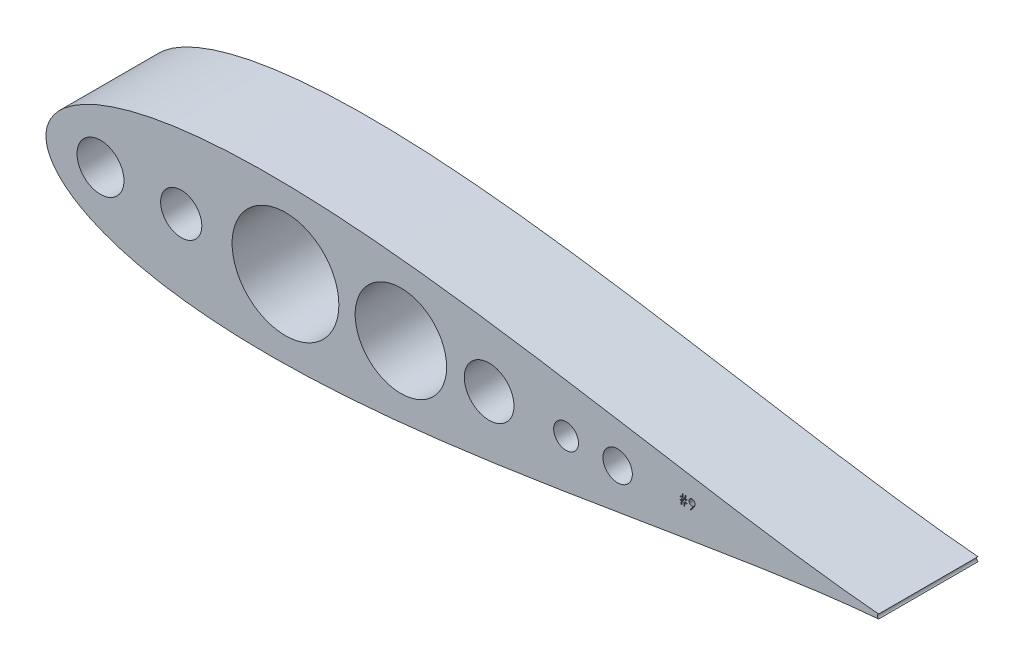
SolidWorks part; units mm, degrees
material "Polyurethane Foam Rigid"
ref_plane "Front Plane" through (0, 0, 0) normal (0, 0, 1) x (1, 0, 0)
ref_plane "Top Plane" through (0, 0, 0) normal (0, 1, 0) x (1, 0, 0)
ref_plane "Right Plane" through (0, 0, 0) normal (1, 0, 0) x (0, 0, -1)
sketch "Sketch2" plane through (0, 0, 0) normal (0, 0, 1) x (1, 0, 0)
  line L0 (258.6504, 1.1911) -> (258.6504, 0.8654)
  line L1 (258.6504, 0.8654) -> (257.6796, 0.8654)
  line L2 (257.6796, 0.8654) -> (257.416, -0.893)
  line L3 (257.416, -0.893) -> (257.0222, -0.893)
  line L4 (257.0222, -0.893) -> (257.2857, 0.8654)
  line L5 (257.2857, 0.8654) -> (256.2467, 0.8654)
  line L6 (256.2467, 0.8654) -> (255.9832, -0.893)
  line L7 (255.9832, -0.893) -> (255.5893, -0.893)
  line L8 (255.5893, -0.893) -> (255.8529, 0.8654)
  line L9 (255.8529, 0.8654) -> (255.0032, 0.8654)
  line L10 (255.0032, 0.8654) -> (255.0032, 1.1911)
  line L11 (255.0032, 1.1911) -> (255.9018, 1.1911)
  line L12 (255.9018, 1.1911) -> (256.0778, 2.3634)
  line L13 (256.0778, 2.3634) -> (255.1334, 2.3634)
  line L14 (255.1334, 2.3634) -> (255.1334, 2.689)
  line L15 (255.1334, 2.689) -> (256.1267, 2.689)
  line L16 (256.1267, 2.689) -> (256.3709, 4.3172)
  line L17 (256.3709, 4.3172) -> (256.7637, 4.3172)
  line L18 (256.7637, 4.3172) -> (256.5195, 2.689)
  line L19 (256.5195, 2.689) -> (257.5595, 2.689)
  line L20 (257.5595, 2.689) -> (257.8037, 4.3172)
  line L21 (257.8037, 4.3172) -> (258.1965, 4.3172)
  line L22 (258.1965, 4.3172) -> (257.9523, 2.689)
  line L23 (257.9523, 2.689) -> (258.7806, 2.689)
  line L24 (258.7806, 2.689) -> (258.7806, 2.3634)
  line L25 (258.7806, 2.3634) -> (257.9034, 2.3634)
  line L26 (257.9034, 2.3634) -> (257.7284, 1.1911)
  line L27 (257.7284, 1.1911) -> (258.6504, 1.1911)
  line L28 (257.5106, 2.3634) -> (256.4706, 2.3634)
  line L29 (256.4706, 2.3634) -> (256.2956, 1.1911)
  line L30 (256.2956, 1.1911) -> (257.3346, 1.1911)
  line L31 (257.3346, 1.1911) -> (257.5106, 2.3634)
  line L32 (260.7345, -1.0233) -> (260.3702, -0.7699)
  line L33 (260.3702, -0.7699) -> (261.7826, 1.2949)
  line L34 (261.7826, 1.2949) -> (261.5119, 1.2664)
  line L35 (261.5119, 1.2664) -> (261.2484, 1.2562)
  line L36 (261.2484, 1.2562) -> (261.0886, 1.2633)
  line L37 (261.0886, 1.2633) -> (260.936, 1.2837)
  line L38 (260.936, 1.2837) -> (260.7884, 1.3173)
  line L39 (260.7884, 1.3173) -> (260.648, 1.3651)
  line L40 (260.648, 1.3651) -> (260.5126, 1.4262)
  line L41 (260.5126, 1.4262) -> (260.3844, 1.5004)
  line L42 (260.3844, 1.5004) -> (260.2613, 1.589)
  line L43 (260.2613, 1.589) -> (260.1453, 1.6907)
  line L44 (260.1453, 1.6907) -> (260.0394, 1.8027)
  line L45 (260.0394, 1.8027) -> (259.9468, 1.9207)
  line L46 (259.9468, 1.9207) -> (259.8695, 2.0449)
  line L47 (259.8695, 2.0449) -> (259.8054, 2.1762)
  line L48 (259.8054, 2.1762) -> (259.7565, 2.3125)
  line L49 (259.7565, 2.3125) -> (259.7209, 2.456)
  line L50 (259.7209, 2.456) -> (259.6995, 2.6056)
  line L51 (259.6995, 2.6056) -> (259.6924, 2.7613)
  line L52 (259.6924, 2.7613) -> (259.7057, 2.974)
  line L53 (259.7057, 2.974) -> (259.7443, 3.1755)
  line L54 (259.7443, 3.1755) -> (259.8095, 3.3668)
  line L55 (259.8095, 3.3668) -> (259.9, 3.5469)
  line L56 (259.9, 3.5469) -> (260.015, 3.7138)
  line L57 (260.015, 3.7138) -> (260.1514, 3.8624)
  line L58 (260.1514, 3.8624) -> (260.3101, 3.9936)
  line L59 (260.3101, 3.9936) -> (260.4902, 4.1076)
  line L60 (260.4902, 4.1076) -> (260.6846, 4.1992)
  line L61 (260.6846, 4.1992) -> (260.8861, 4.2653)
  line L62 (260.8861, 4.2653) -> (261.0947, 4.304)
  line L63 (261.0947, 4.304) -> (261.3094, 4.3172)
  line L64 (261.3094, 4.3172) -> (261.5201, 4.304)
  line L65 (261.5201, 4.304) -> (261.7226, 4.2664)
  line L66 (261.7226, 4.2664) -> (261.917, 4.2022)
  line L67 (261.917, 4.2022) -> (262.1032, 4.1127)
  line L68 (262.1032, 4.1127) -> (262.2762, 3.9997)
  line L69 (262.2762, 3.9997) -> (262.4288, 3.8674)
  line L70 (262.4288, 3.8674) -> (262.5621, 3.7138)
  line L71 (262.5621, 3.7138) -> (262.6761, 3.5398)
  line L72 (262.6761, 3.5398) -> (262.7667, 3.3535)
  line L73 (262.7667, 3.3535) -> (262.8318, 3.1602)
  line L74 (262.8318, 3.1602) -> (262.8705, 2.9618)
  line L75 (262.8705, 2.9618) -> (262.8837, 2.7562)
  line L76 (262.8837, 2.7562) -> (262.8756, 2.5964)
  line L77 (262.8756, 2.5964) -> (262.8522, 2.4336)
  line L78 (262.8522, 2.4336) -> (262.8115, 2.2657)
  line L79 (262.8115, 2.2657) -> (262.7555, 2.0947)
  line L80 (262.7555, 2.0947) -> (262.7209, 2.0062)
  line L81 (262.7209, 2.0062) -> (262.6792, 1.9136)
  line L82 (262.6792, 1.9136) -> (262.6313, 1.8159)
  line L83 (262.6313, 1.8159) -> (262.5774, 1.7152)
  line L84 (262.5774, 1.7152) -> (262.5174, 1.6083)
  line L85 (262.5174, 1.6083) -> (262.4512, 1.4984)
  line L86 (262.4512, 1.4984) -> (262.3779, 1.3834)
  line L87 (262.3779, 1.3834) -> (262.2986, 1.2644)
  line L88 (262.2986, 1.2644) -> (260.7345, -1.0233)
  line L89 (261.3328, 1.7772) -> (261.4539, 1.7823)
  line L90 (261.4539, 1.7823) -> (261.5679, 1.7956)
  line L91 (261.5679, 1.7956) -> (261.6768, 1.819)
  line L92 (261.6768, 1.819) -> (261.7786, 1.8515)
  line L93 (261.7786, 1.8515) -> (261.8752, 1.8922)
  line L94 (261.8752, 1.8922) -> (261.9658, 1.9431)
  line L95 (261.9658, 1.9431) -> (262.0492, 2.0032)
  line L96 (262.0492, 2.0032) -> (262.1276, 2.0724)
  line L97 (262.1276, 2.0724) -> (262.1978, 2.1487)
  line L98 (262.1978, 2.1487) -> (262.2589, 2.228)
  line L99 (262.2589, 2.228) -> (262.3108, 2.3115)
  line L100 (262.3108, 2.3115) -> (262.3525, 2.399)
  line L101 (262.3525, 2.399) -> (262.3861, 2.4906)
  line L102 (262.3861, 2.4906) -> (262.4095, 2.5852)
  line L103 (262.4095, 2.5852) -> (262.4227, 2.6839)
  line L104 (262.4227, 2.6839) -> (262.4278, 2.7867)
  line L105 (262.4278, 2.7867) -> (262.4227, 2.8895)
  line L106 (262.4227, 2.8895) -> (262.4075, 2.9882)
  line L107 (262.4075, 2.9882) -> (262.381, 3.0829)
  line L108 (262.381, 3.0829) -> (262.3444, 3.1744)
  line L109 (262.3444, 3.1744) -> (262.2976, 3.2609)
  line L110 (262.2976, 3.2609) -> (262.2406, 3.3444)
  line L111 (262.2406, 3.3444) -> (262.1724, 3.4248)
  line L112 (262.1724, 3.4248) -> (262.094, 3.5001)
  line L113 (262.094, 3.5001) -> (262.0085, 3.5693)
  line L114 (262.0085, 3.5693) -> (261.919, 3.6293)
  line L115 (261.919, 3.6293) -> (261.8244, 3.6802)
  line L116 (261.8244, 3.6802) -> (261.7256, 3.7219)
  line L117 (261.7256, 3.7219) -> (261.6229, 3.7545)
  line L118 (261.6229, 3.7545) -> (261.515, 3.7779)
  line L119 (261.515, 3.7779) -> (261.4031, 3.7911)
  line L120 (261.4031, 3.7911) -> (261.286, 3.7962)
  line L121 (261.286, 3.7962) -> (261.17, 3.7911)
  line L122 (261.17, 3.7911) -> (261.0591, 3.7779)
  line L123 (261.0591, 3.7779) -> (260.9522, 3.7545)
  line L124 (260.9522, 3.7545) -> (260.8495, 3.7219)
  line L125 (260.8495, 3.7219) -> (260.7508, 3.6802)
  line L126 (260.7508, 3.6802) -> (260.6561, 3.6293)
  line L127 (260.6561, 3.6293) -> (260.5666, 3.5693)
  line L128 (260.5666, 3.5693) -> (260.4811, 3.5001)
  line L129 (260.4811, 3.5001) -> (260.4027, 3.4248)
  line L130 (260.4027, 3.4248) -> (260.3356, 3.3444)
  line L131 (260.3356, 3.3444) -> (260.2786, 3.2609)
  line L132 (260.2786, 3.2609) -> (260.2318, 3.1744)
  line L133 (260.2318, 3.1744) -> (260.1951, 3.0829)
  line L134 (260.1951, 3.0829) -> (260.1687, 2.9882)
  line L135 (260.1687, 2.9882) -> (260.1534, 2.8895)
  line L136 (260.1534, 2.8895) -> (260.1483, 2.7867)
  line L137 (260.1483, 2.7867) -> (260.1534, 2.6839)
  line L138 (260.1534, 2.6839) -> (260.1697, 2.5852)
  line L139 (260.1697, 2.5852) -> (260.1972, 2.4906)
  line L140 (260.1972, 2.4906) -> (260.2348, 2.399)
  line L141 (260.2348, 2.399) -> (260.2837, 2.3115)
  line L142 (260.2837, 2.3115) -> (260.3437, 2.228)
  line L143 (260.3437, 2.228) -> (260.4139, 2.1487)
  line L144 (260.4139, 2.1487) -> (260.4953, 2.0724)
  line L145 (260.4953, 2.0724) -> (260.5839, 2.0032)
  line L146 (260.5839, 2.0032) -> (260.6775, 1.9431)
  line L147 (260.6775, 1.9431) -> (260.7762, 1.8922)
  line L148 (260.7762, 1.8922) -> (260.878, 1.8515)
  line L149 (260.878, 1.8515) -> (260.9848, 1.819)
  line L150 (260.9848, 1.819) -> (261.0967, 1.7956)
  line L151 (261.0967, 1.7956) -> (261.2128, 1.7823)
  line L152 (261.2128, 1.7823) -> (261.3328, 1.7772)
  circle A0 centre (-41.275, 0) radius 12.0033
  circle A1 centre (0, 0) radius 10.541
  circle A2 centre (53.338, 0) radius 27.3042
  circle A3 centre (157.48, 0) radius 12.7
  circle A4 centre (223.2139, 0) radius 7.5268
  circle A5 centre (112.3573, 0) radius 23.3878
  arc A6 (356.7188, 1.1142) -> (356.7188, -1.1142) centre (357.2733, 0) ccw
  circle A7 centre (196.85, 0) radius 6.35
  spline S0 degree 3 poles (356.7188, 1.1142) (356.0338, 1.1732) (354.6472, 1.2925) (352.5436, 1.4844) (350.3911, 1.6885) (348.1899, 1.9056) (345.9398, 2.1355) (342.1802, 2.5322) (336.8158, 3.133) (329.9757, 3.9576) (323.0336, 4.8458) (313.8615, 6.0788) (302.3587, 7.7237) (288.6337, 9.805) (274.9221, 11.9724) (261.2201, 14.1999) (249.8068, 16.0865) (240.6774, 17.6031) (231.5482, 19.1212) (220.1361, 21.015) (206.4373, 23.2615) (192.7309, 25.462) (179.0142, 27.5966) (160.7077, 30.3278) (137.7851, 33.474) (110.2003, 36.6385) (87.0321, 38.5983) (68.5494, 39.6067) (54.5511, 40.05) (40.7774, 40.1228) (26.7493, 39.7655) (13.012, 38.9182) (-0.7973, 37.4621) (-12.0839, 35.6753) (-21.1417, 33.7674) (-27.9463, 32.0558) (-34.5959, 30.0529) (-41.1272, 27.6907) (-47.4261, 24.9354) (-53.538, 21.6252) (-58.3357, 18.2887) (-61.8002, 15.2095) (-64.1916, 12.6295) (-66.2213, 9.8466) (-67.8427, 6.7607) (-68.8989, 3.4741) (-69.2739, 0) (-68.8989, -3.4741) (-67.8427, -6.7606) (-66.2214, -9.8464) (-64.1918, -12.6293) (-61.8003, -15.2094) (-58.3359, -18.2886) (-53.538, -21.6252) (-47.4261, -24.9354) (-41.1274, -27.6906) (-34.5961, -30.0528) (-27.9465, -32.0558) (-21.1417, -33.7674) (-12.0839, -35.6753) (-0.7975, -37.4621) (13.0118, -38.9182) (26.749, -39.7655) (40.7772, -40.1228) (54.5508, -40.05) (68.5492, -39.6067) (87.0319, -38.5983) (110.2003, -36.6385) (137.7851, -33.474) (160.7077, -30.3278) (179.0142, -27.5966) (192.7309, -25.462) (206.4373, -23.2615) (220.1361, -21.015) (231.5482, -19.1212) (240.6774, -17.6031) (249.8068, -16.0865) (261.2201, -14.1999) (274.9221, -11.9724) (288.6337, -9.805) (302.3587, -7.7237) (313.8613, -6.0788) (323.0334, -4.8458) (329.9754, -3.9576) (336.8157, -3.1331) (342.9292, -2.4482) (348.1398, -1.9072) (352.4934, -1.4831) (355.3323, -1.2353) (356.7188, -1.1142) knots 0 0 0 0 0.002326 0.004707 0.007145 0.009639 0.012189 0.014795 0.022426 0.030447 0.038099 0.046099 0.06175 0.077401 0.093053 0.108704 0.124356 0.132182 0.140007 0.155659 0.17131 0.186962 0.202613 0.218265 0.249567 0.28087 0.312172 0.328195 0.343475 0.359539 0.374777 0.390931 0.40608 0.421731 0.429557 0.437383 0.445457 0.453036 0.460863 0.46869 0.476515 0.480564 0.484347 0.488394 0.492178 0.496091 0.5 0.503909 0.507822 0.511605 0.515653 0.519435 0.523485 0.53131 0.539137 0.546964 0.554542 0.562617 0.570443 0.578269 0.59392 0.609068 0.625223 0.64046 0.656525 0.671805 0.687828 0.71913 0.750433 0.781735 0.797387 0.813038 0.82869 0.844341 0.859993 0.867818 0.875644 0.891296 0.906947 0.922599 0.93825 0.953901 0.961901 0.969553 0.977573 0.985205 0.990361 0.995293 1 1 1 1
other "AlignGroup1"
other "AlignGroup2" parameters "D1"=34.544, "D2"=54.6083, "D3"=54.6083
extrude "Boss-Extrude1" add sketch "Sketch2" along normal blind 50.8 contours A6 S0 L87 L88 L32 L33 L34 L35 L36 L37 L38 L39 L40 L41 L42 L43 L44 L45 L46 L47 L48 L49 L50 L51 L52 L53 L54 L55 L56 L57 L58 L59 L60 L61 L62 L63 L64 L65 L66 L67 L68 L69 L70 L71 L72 L73 L74 L75 L76 L77
equation "\"MastDiam\"= .83"
